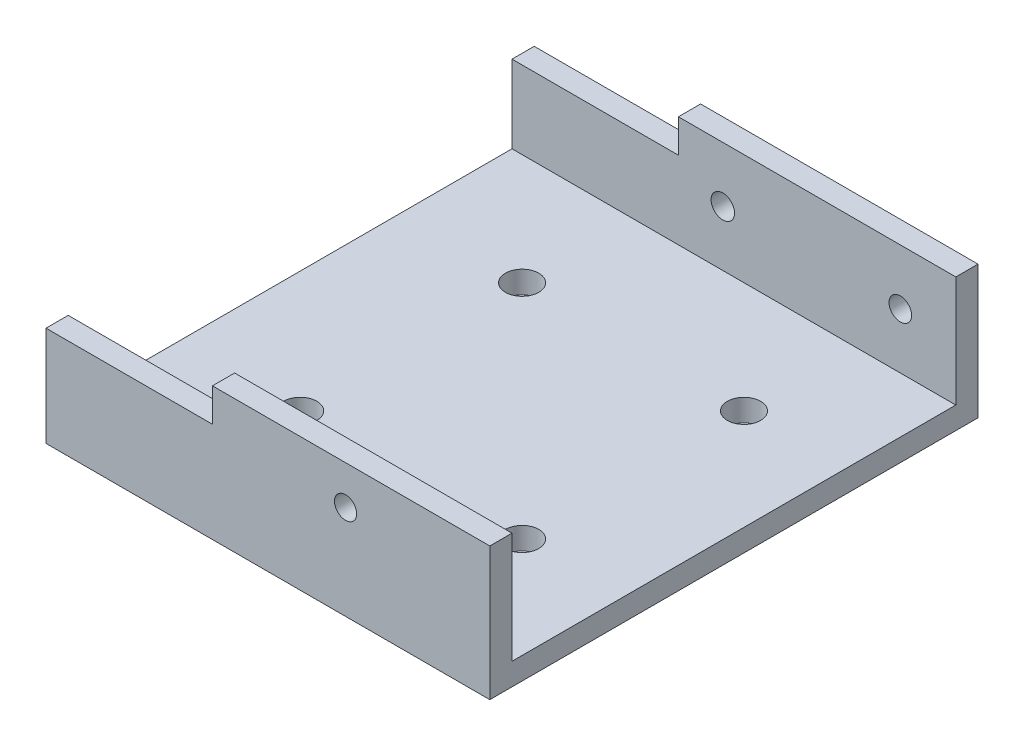
SolidWorks part; units mm, degrees
ref_plane "Front Plane" through (0, 0, 0) normal (0, 0, 1) x (1, 0, 0)
ref_plane "Top Plane" through (0, 0, 0) normal (0, 1, 0) x (1, 0, 0)
ref_plane "Right Plane" through (0, 0, 0) normal (1, 0, 0) x (0, 0, -1)
sketch "Sketch1" plane through (0, 0, 0) normal (0, 1, 0) x (1, 0, 0)
  line L1 (0, 0) -> (40, 0)
  line L2 (0, 0) -> (0, 44)
  line L3 (0, 44) -> (40, 44)
  line L4 (40, 0) -> (40, 44)
  dimension "D1" = 40
  dimension "D2" = 44
extrude "Boss-Extrude1" add sketch "Sketch1" along normal blind 2
sketch "Sketch2" plane through (0, 2, 0) normal (0, 1, 0) x (1, 0, 0)
  line L0 (40, 0) -> (40, 44) construction
  line L1 (0, 44) -> (40, 44)
  line L2 (0, 44) -> (0, 42)
  line L3 (0, 42) -> (40, 42)
  line L4 (40, 44) -> (40, 42)
  line L6 (0, 0) -> (40, 0)
  line L7 (0, 0) -> (0, 2)
  line L8 (0, 2) -> (40, 2)
  line L9 (40, 0) -> (40, 2)
  dimension "D1" = 2
  dimension "D2" = 2
extrude "Boss-Extrude2" add sketch "Sketch2" along normal blind 10
sketch "Sketch3" plane through (0, 0, -44) normal (0, 0, -1) x (-1, 0, 0)
  line L1 (0, 12) -> (-15, 12)
  line L2 (0, 12) -> (0, 9)
  line L3 (0, 9) -> (-15, 9)
  line L4 (-15, 12) -> (-15, 9)
  dimension "D1" = 3
  dimension "D2" = 15
extrude "Cut-Extrude2" cut sketch "Sketch3" against normal through all
sketch "Sketch4" plane through (0, 0, -42) normal (0, 0, -1) x (-1, 0, 0)
  circle A0 centre (-35, 7) radius 1.0172
  circle A1 centre (-19, 7) radius 1.0565
extrude "Cut-Extrude3" cut sketch "Sketch4" along normal up to next
sketch "Sketch5" plane through (0, 0, 0) normal (0, 0, 1) x (1, 0, 0)
  circle A0 centre (27, 8.5) radius 1
  dimension "D1" = 2
extrude "Cut-Extrude4" cut sketch "Sketch5" against normal up to next
sketch "Sketch6" plane through (0, 0, 0) normal (0, -1, 0) x (1, 0, 0)
  line L0 (0, -44) -> (40, 0) construction
  line L1 (0, 0) -> (40, -44) construction
  circle A0 centre (10.9091, -32) radius 1.5
  circle A1 centre (10.9091, -12) radius 1.5
  circle A2 centre (30.9091, -12) radius 1.5
  circle A3 centre (30.9091, -32) radius 1.5
  dimension "D1" = 3
  dimension "D2" = 3
  dimension "D3" = 3
  dimension "D4" = 3
  dimension "D5" = 20
  dimension "D6" = 20
  dimension "D7" = 20
extrude "Cut-Extrude5" cut sketch "Sketch6" against normal up to next
